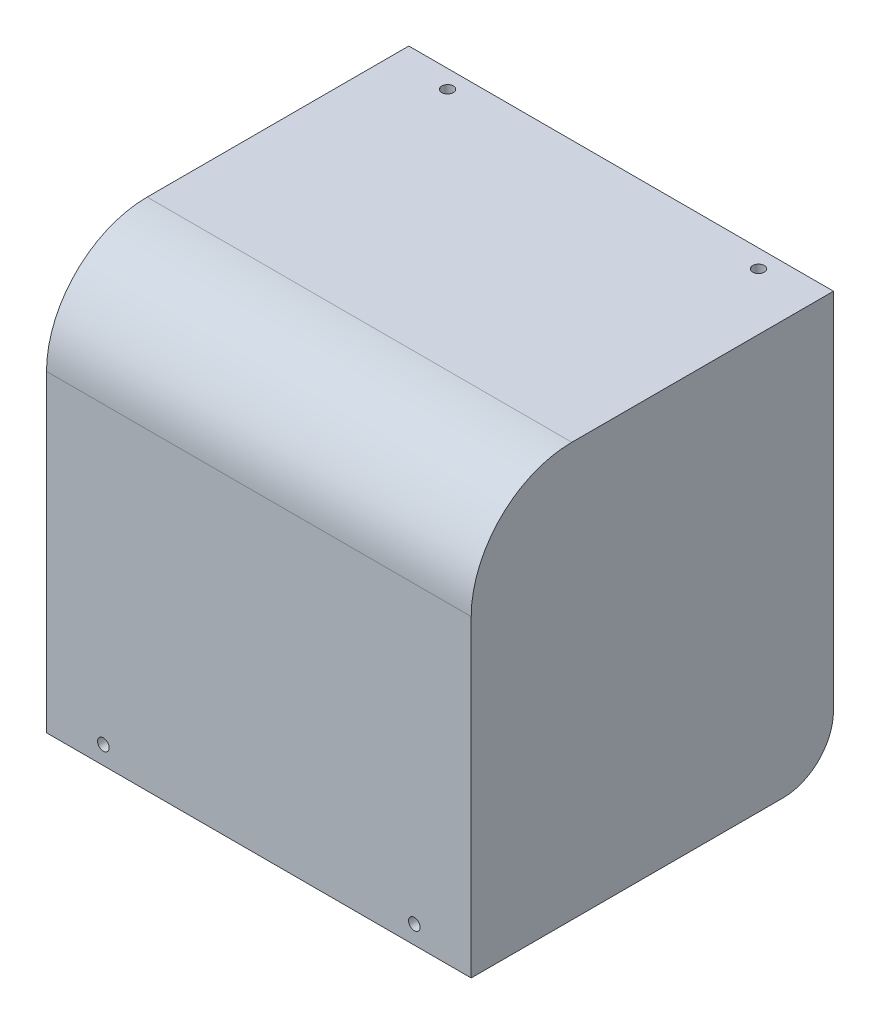
SolidWorks part; units mm, degrees
ref_plane "Front Plane" through (0, 0, 0) normal (0, 0, 1) x (1, 0, 0)
ref_plane "Top Plane" through (0, 0, 0) normal (0, 1, 0) x (1, 0, 0)
ref_plane "Right Plane" through (0, 0, 0) normal (1, 0, 0) x (0, 0, -1)
sketch "Sketch1" plane through (0, 0, 0) normal (1, 0, 0) x (0, 0, -1)
  line L0 (0, 0) -> (0, 82.2)
  line L1 (0, 82.2) -> (72, 82.2)
  line L2 (72, 82.2) -> (72, 80.2)
  line L3 (72, 80.2) -> (2, 80.2)
  line L4 (2, 80.2) -> (2, 0)
  line L5 (2, 0) -> (0, 0)
  dimension "D1" = 80.2
  dimension "D2" = 70
  dimension "D3" = 2
  dimension "D4" = 2
extrude "Boss-Extrude1" add sketch "Sketch1" along normal mid plane 84.4
sketch "Sketch2" plane through (0, 0, 0) normal (0, 0, 1) x (1, 0, 0)
  line L0 (-42.2, 3.64) -> (42.2, 3.64) construction
  line L1 (-42.2, 82.2) -> (-42.2, 0) construction
  line L2 (42.2, 82.2) -> (42.2, 0) construction
  line L3 (0, 3.64) -> (0, 0) construction
  line L4 (42.2, 0) -> (-42.2, 0) construction
  circle A0 centre (-30.9, 3.64) radius 1.15
  circle A1 centre (30.9, 3.64) radius 1.15
  dimension "D2" = 2.3
  dimension "D1" = 61.8
  dimension "D3" = 3.64
extrude "Cut-Extrude1" cut sketch "Sketch2" against normal blind 70
fillet "Fillet1" radius 20 2 edges at (0, 82.2, 0) (0, 80.2, -2)
sketch "Sketch3" plane through (-42.2, 0, 0) normal (-1, 0, 0) x (0, 0, 1)
  line L0 (-72, 80.2) -> (-72, 0)
  line L1 (-72, 0) -> (-2, 0)
  line L2 (-2, 0) -> (-2, 60.2) construction
  line L3 (-22, 80.2) -> (-72, 80.2) construction
  line L4 (-2, 0) -> (-2, 60.2)
  line L5 (-22, 80.2) -> (-72, 80.2)
  arc A0 (-2, 60.2) -> (-22, 80.2) centre (-22, 60.2) ccw construction
  arc A1 (-2, 60.2) -> (-22, 80.2) centre (-22, 60.2) ccw
extrude "Boss-Extrude2" add sketch "Sketch3" against normal blind 2
mirror "Mirror1" about plane through (0, 0, 0) normal (1, 0, 0) of "Boss-Extrude2"
fillet "Fillet2" radius 10 2 edges at (-41.2, 0, -72) (41.2, 0, -72)
sketch "Sketch4" plane through (0, 82.2, 0) normal (0, 1, 0) x (1, 0, 0)
  line L0 (-42.2, 68.402) -> (42.2, 68.402) construction
  line L1 (0, 68.402) -> (0, 72) construction
  line L2 (42.2, 72) -> (42.2, 20) construction
  line L3 (-42.2, 72) -> (-42.2, 20) construction
  line L4 (42.2, 72) -> (-42.2, 72) construction
  circle A0 centre (-30.9, 68.402) radius 1.15
  circle A1 centre (30.9, 68.402) radius 1.15
  point P8 (42.2, 62.541)
  point P11 (-42.2, 62.792)
  point P14 (0, 72)
  dimension "D1" = 2.3
  dimension "D2" = 61.8
  dimension "D3" = 3.598
extrude "Cut-Extrude2" cut sketch "Sketch4" against normal blind 10
